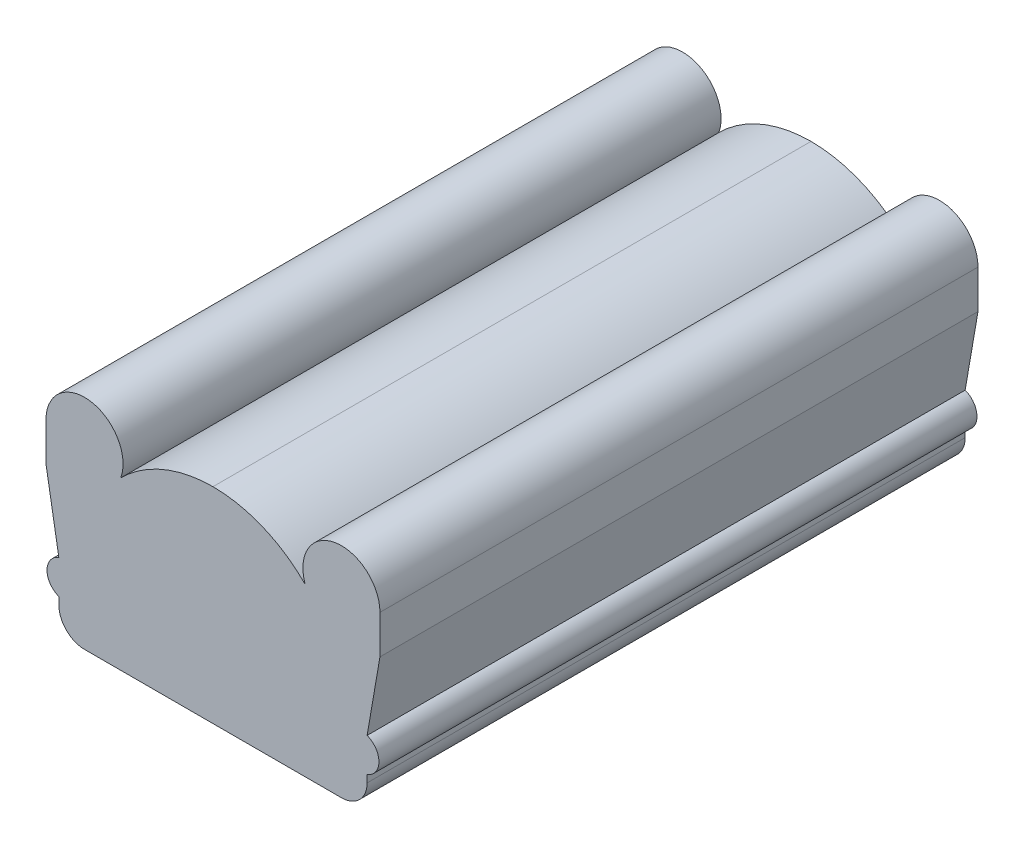
SolidWorks part; units mm, degrees
ref_plane "Front Plane" through (0, 0, 0) normal (0, 0, 1) x (1, 0, 0)
ref_plane "Top Plane" through (0, 0, 0) normal (0, 1, 0) x (1, 0, 0)
ref_plane "Right Plane" through (0, 0, 0) normal (1, 0, 0) x (0, 0, -1)
sketch "Sketch1" plane through (0, 0, 0) normal (0, 0, 1) x (1, 0, 0)
  line L0 (76.2, 107.95) -> (0, 107.95) construction
  line L1 (76.2, 0) -> (76.2, 107.95) construction
  line L2 (0, 0) -> (76.2, 0) construction
  line L3 (82.55, 88.9) -> (82.55, 69.85)
  line L4 (0, 0) -> (0, 144.1487) construction
  line L5 (82.55, 69.85) -> (76.2, 69.85) construction
  line L6 (76.2, 0) -> (-76.2, 0)
  line L7 (63.5, 88.9) -> (76.2, 88.9) construction
  line L8 (63.5, 88.9) -> (45.5989, 82.3845) construction
  line L9 (76.2, 69.85) -> (76.2, 63.5) construction
  line L10 (45.5989, 82.3845) -> (0, 82.3845) construction
  line L11 (82.55, 69.85) -> (76.2, 33.02)
  line L13 (76.2, 16.3177) -> (76.2, 0)
  line L14 (0, 82.3845) -> (-45.5989, 82.3845) construction
  line L15 (-76.2, 16.3177) -> (-76.2, 0)
  line L16 (-82.55, 69.85) -> (-76.2, 33.02)
  line L17 (-82.55, 88.9) -> (-82.55, 69.85)
  arc A0 (45.5989, 82.3845) -> (82.55, 88.9) centre (63.5, 88.9) cw
  arc A1 (76.2, 33.02) -> (76.2, 16.3177) centre (73.152, 24.6688) cw
  circle A2 centre (63.5, 88.9) radius 19.05 construction
  arc A3 (45.5989, 82.3845) -> (0, 101.4345) centre (-0.162, 36.9482) ccw
  arc A4 (-76.2, 33.02) -> (-76.2, 16.3177) centre (-73.152, 24.6688) ccw
  arc A5 (-45.5989, 82.3845) -> (-82.55, 88.9) centre (-63.5, 88.9) ccw
  arc A6 (-45.5989, 82.3845) -> (0, 101.4345) centre (0.162, 36.9482) cw
  point P9 (76.2, 88.9)
  point P13 (63.5, 107.95)
  point P14 (63.5, 88.9)
  point P23 (24.6967, 96.4508)
  point P24 (0, 0)
  point P26 (0, 107.95)
  point P27 (76.2, 8.1588)
  point P29 (-76.2, 8.1588)
  dimension "D4" = 38.1
  dimension "D9" = 8.89
  dimension "D1" = 76.2
  dimension "D2" = 12.7
  dimension "D3" = 107.95
  dimension "D5" = 200
  dimension "D6" = 19.05
  dimension "D7" = 19.05
  dimension "D8" = 30.48
  dimension "D10" = 3.048
  dimension "D11" = 19.05
extrude "Boss-Extrude1" add sketch "Sketch1" along normal blind 295.656
fillet "Fillet1" radius 12.7 2 edges at (-76.2, 0, 147.828) (76.2, 0, 147.828)
